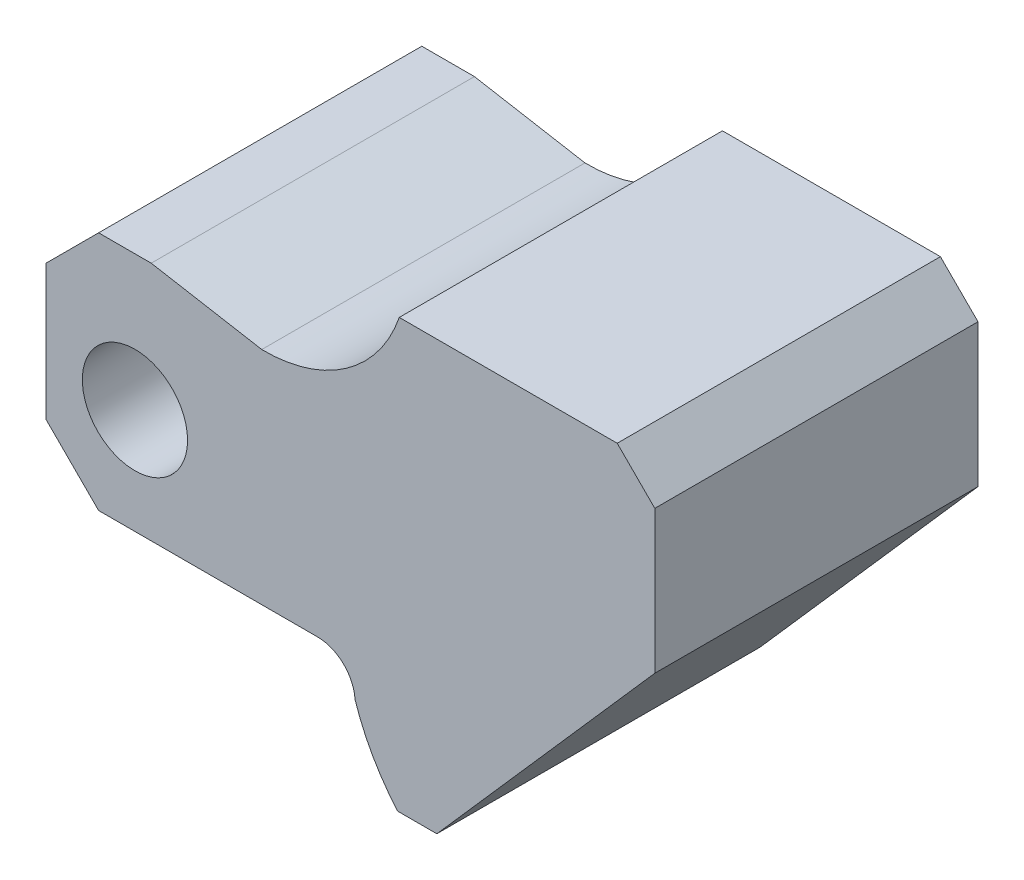
SolidWorks part; units mm, degrees
material "AISI 1020"
ref_plane "Plan de face" through (0, 0, 0) normal (0, 0, 1) x (1, 0, 0)
ref_plane "Plan de dessus" through (0, 0, 0) normal (0, 1, 0) x (1, 0, 0)
ref_plane "Plan de droite" through (0, 0, 0) normal (1, 0, 0) x (0, 0, -1)
sketch "Esquisse1" plane through (0, 0, 0) normal (0, 0, 1) x (1, 0, 0)
  line L15 (71.0555, 42.5858) -> (100.0555, 42.5858)
  line L16 (100.0555, 42.5858) -> (105.0555, 37.5858)
  line L17 (105.0555, 37.5858) -> (105.0555, 18.5858)
  line L20 (105.0555, 18.5858) -> (76.0555, -14.4142)
  line L24 (38.0555, 32.334) -> (52.7651, 29.7403)
  line L25 (38.0555, 32.334) -> (31.0555, 32.334)
  line L26 (31.0555, 32.334) -> (24.0555, 25.334)
  line L30 (24.0555, 25.334) -> (24.0555, 7.334)
  line L31 (24.0555, 7.334) -> (31.0555, 0.334)
  line L32 (31.0555, 0.334) -> (60.1798, 0.334)
  line L33 (76.0555, -14.4142) -> (70.8436, -14.4142)
  arc A4 (71.0555, 42.5858) -> (52.7651, 29.7403) centre (53.079, 48.7377) cw
  arc A6 (60.1798, 0.334) -> (65.1713, -4.3741) centre (60.1798, -4.666) cw
  arc A7 (65.1713, -4.3741) -> (70.8436, -14.4142) centre (92.7525, 4.5858) ccw
  point P7 (92.7525, 4.5858)
  dimension "D8" = 5
  dimension "D9" = 81
  dimension "D6" = 19
  dimension "D15" = 19
  dimension "D10" = 45
  dimension "D12" = 32
  dimension "D2" = 45
  dimension "D3" = 5
  dimension "D4" = 24
  dimension "D5" = 29
  dimension "D7" = 57
  dimension "D11" = 7
  dimension "D16" = 29
  dimension "D19" = 7
  dimension "D20" = 14
  dimension "D21" = 10
extrude "Boss.-Extru.1" add sketch "Esquisse1" along normal blind 43
sketch "Esquisse2" plane through (0, 0, 43) normal (0, 0, 1) x (1, 0, 0)
  line L0 (24.0555, 25.334) -> (24.0555, 7.334) construction
  line L1 (31.0555, 0.334) -> (60.1798, 0.334) construction
  circle A0 centre (35.8885, 14.334) radius 7
  dimension "D1" = 14
  dimension "D2" = 11.833
  dimension "D3" = 14
extrude "Enlèv. mat.-Extru.1" cut sketch "Esquisse2" against normal blind 43
